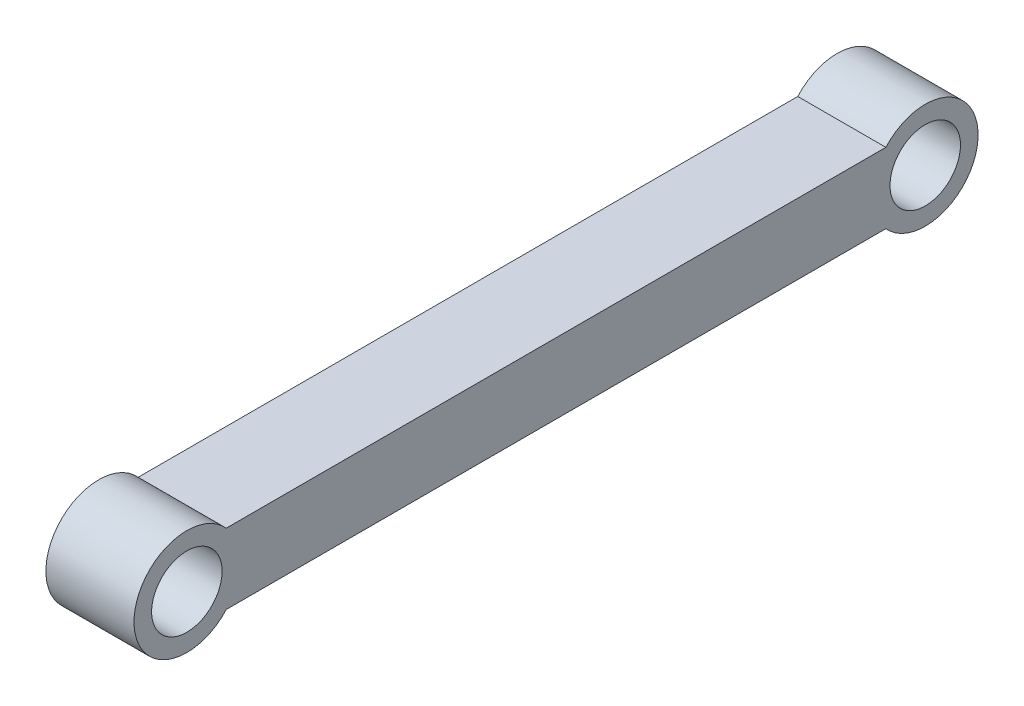
SolidWorks part; units mm, degrees
material "Thornel Mat VMA"
ref_plane "Front Plane" through (0, 0, 0) normal (0, 0, 1) x (1, 0, 0)
ref_plane "Top Plane" through (0, 0, 0) normal (0, 1, 0) x (1, 0, 0)
ref_plane "Right Plane" through (0, 0, 0) normal (1, 0, 0) x (0, 0, -1)
sketch "LinkFrame" plane through (0, 0, 0) normal (1, 0, 0) x (0, 0, -1)
  line L0 (-578.5355, -226.2633) -> (259.6545, -226.2633) construction
  line L1 (-533.8142, -186.2633) -> (214.9331, -186.2633)
  line L2 (-533.8142, -266.2633) -> (214.9331, -266.2633)
  arc A1 (214.9331, -266.2633) -> (214.9331, -186.2633) centre (259.6545, -226.2633) ccw
  arc A2 (-533.8142, -186.2633) -> (-533.8142, -266.2633) centre (-578.5355, -226.2633) ccw
  circle A5 centre (-578.5355, -226.2633) radius 40
  circle A6 centre (259.6545, -226.2633) radius 40
  dimension "D1" = 120
  dimension "D2" = 120
  dimension "D5" = 80
  dimension "D6" = 80
  dimension "D3" = 838.19
  dimension "D4" = 80
  dimension "D7" = 44.7214
  dimension "D8" = 44.7214
extrude "Boss-Extrude1" add sketch "LinkFrame" along normal blind 100
equation "\"D1@LinkFrame\" = 1.5 * \"HoleMountDiameter@PrintingPress.Assembly\""
equation "\"D2@LinkFrame\" = 1.5 * \"HoleMountDiameter@PrintingPress.Assembly\""
equation "\"LinkLength\"= 60cm + 23.819cm"
equation "\"D3@LinkFrame\" = \"LinkLength\""
equation "\"D4@LinkFrame\" = \"HoleMountDiameter@PrintingPress.Assembly\""
equation "\"D5@LinkFrame\"=\"HoleMountDiameter@PrintingPress.Assembly\""
equation "\"D6@LinkFrame\"=\"HoleMountDiameter@PrintingPress.Assembly\""
equation "\"D1@Boss-Extrude1\"=\"RivetLength@PrintingPress.Assembly\""
